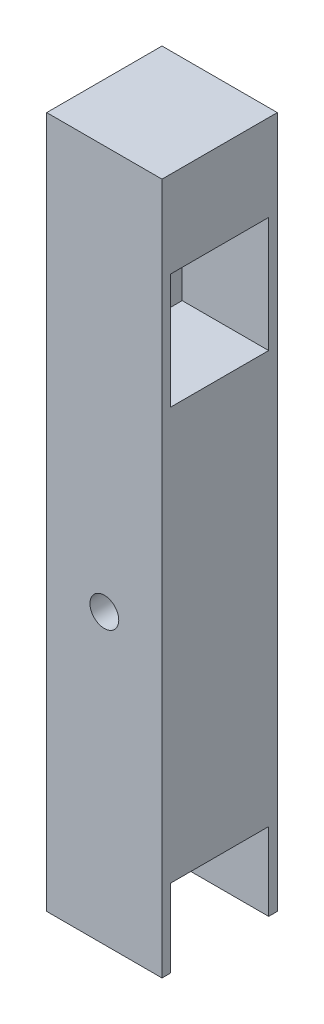
SolidWorks part; units mm, degrees
ref_plane "Front Plane" through (0, 0, 0) normal (0, 0, 1) x (1, 0, 0)
ref_plane "Top Plane" through (0, 0, 0) normal (0, 1, 0) x (1, 0, 0)
ref_plane "Right Plane" through (0, 0, 0) normal (1, 0, 0) x (0, 0, -1)
sketch "Sketch1" plane through (0, 0, 0) normal (0, 0, 1) x (1, 0, 0)
  line L0 (12.7, 63.5) -> (12.7, 0)
  line L1 (0, 0) -> (25.4, 0)
  line L2 (0, 0) -> (0, 152.4)
  line L3 (0, 152.4) -> (25.4, 152.4)
  line L4 (25.4, 0) -> (25.4, 152.4)
  line L5 (25.4, 0) -> (25.4, 71.8853)
  circle A0 centre (12.7, 63.5) radius 3.175
  dimension "D3" = 6.35
  dimension "D1" = 25.4
  dimension "D2" = 152.4
  dimension "D4" = 63.5
extrude "Boss-Extrude1" add sketch "Sketch1" along normal blind 25.4
sketch "Sketch3" plane through (25.4, 0, 0) normal (1, 0, 0) x (0, 0, -1)
  line L0 (-12.7, 120.6525) -> (-12.7, 6.3525)
  line L1 (-12.7, 152.4) -> (-12.7, 120.6525)
  line L2 (-25.4, 152.4) -> (0, 152.4) construction
  circle A4 centre (-12.7, 120.6525) radius 6.35
  circle A5 centre (-12.7, 6.3525) radius 6.35
  point P1 (0, 0)
  point P8 (0, 0)
  point P10 (-12.7, 129.1473)
  dimension "D3" = 12.7
  dimension "D2" = 12.7
  dimension "D1" = 114.3
  dimension "D4" = 31.7475
extrude "Cut-Extrude5" cut sketch "Sketch3" against normal through all
sketch "Sketch5" plane through (25.4, 0, 0) normal (1, 0, 0) x (0, 0, -1)
  line L1 (-23.495, -4.4425) -> (-1.905, -4.4425)
  line L2 (-23.495, -4.4425) -> (-23.495, 17.1475)
  line L3 (-23.495, 17.1475) -> (-1.905, 17.1475)
  line L4 (-1.905, -4.4425) -> (-1.905, 17.1475)
  line L5 (-23.495, -4.4425) -> (-1.905, 17.1475) construction
  line L6 (-23.495, 17.1475) -> (-1.905, -4.4425) construction
  line L12 (-23.495, 107.9525) -> (-1.905, 107.9525)
  line L13 (-23.495, 107.9525) -> (-23.495, 133.3525)
  line L14 (-23.495, 133.3525) -> (-1.905, 133.3525)
  line L15 (-1.905, 107.9525) -> (-1.905, 133.3525)
  line L16 (-23.495, 107.9525) -> (-1.905, 133.3525) construction
  line L17 (-23.495, 133.3525) -> (-1.905, 107.9525) construction
  point P0 (-12.7, 6.3525)
  point P6 (-12.7, 120.6525)
  dimension "D1" = 21.59
  dimension "D2" = 21.59
  dimension "D3" = 21.59
  dimension "D4" = 25.4
extrude "Cut-Extrude6" cut sketch "Sketch5" against normal blind 19.05 contours L13 L12 L15 L14 | L2 L1 L4 L3
